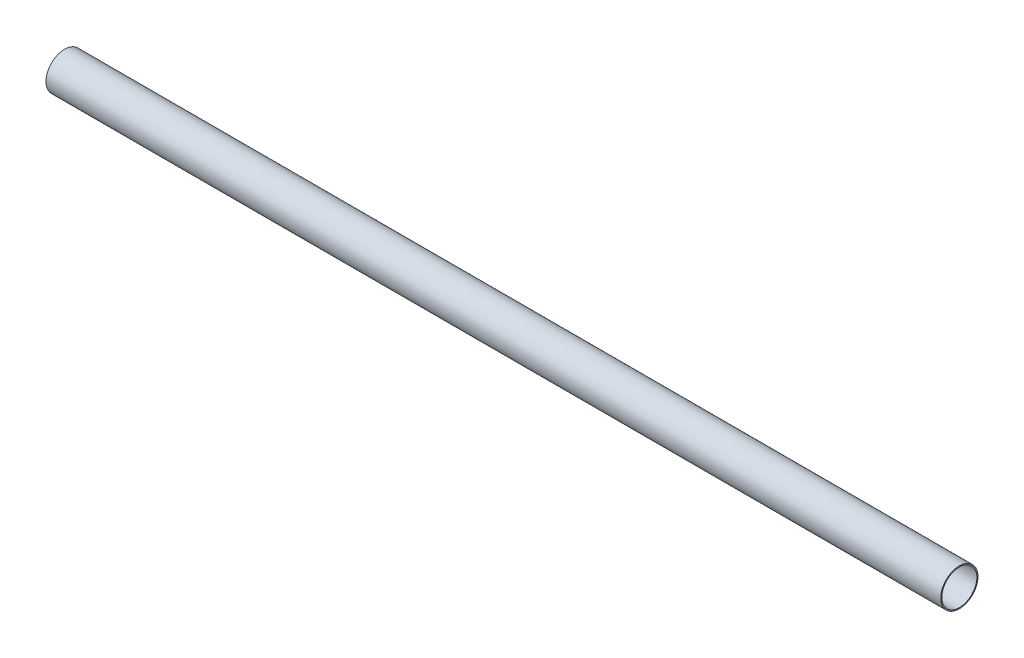
SolidWorks part; units mm, degrees
material "Copper"
ref_plane "Front" through (0, 0, 0) normal (0, 0, 1) x (1, 0, 0)
ref_plane "Top" through (0, 0, 0) normal (0, 1, 0) x (1, 0, 0)
ref_plane "Right" through (0, 0, 0) normal (1, 0, 0) x (0, 0, -1)
sketch "Sketch1" plane through (0, 0, 0) normal (1, 0, 0) x (0, 0, -1)
  circle A0 centre (0, 0) radius 20.6375
  circle A1 centre (0, 0) radius 19.3929
  point P4 (20.6375, 0)
  point P5 (19.3929, 0)
  dimension "OD" = 41.275
  dimension "ID" = 38.7858
  dimension "Wall" = 1.2446
extrude "Extrude1" add sketch "Sketch1" along normal mid plane 990.6
sketch "Sketch2" plane through (0, 0, 0) normal (0, 0, 1) x (1, 0, 0)
  line L0 (-495.3, 0) -> (495.3, 0) construction
  line L1 (-495.3, 20.6375) -> (-495.3, -20.6375) construction
